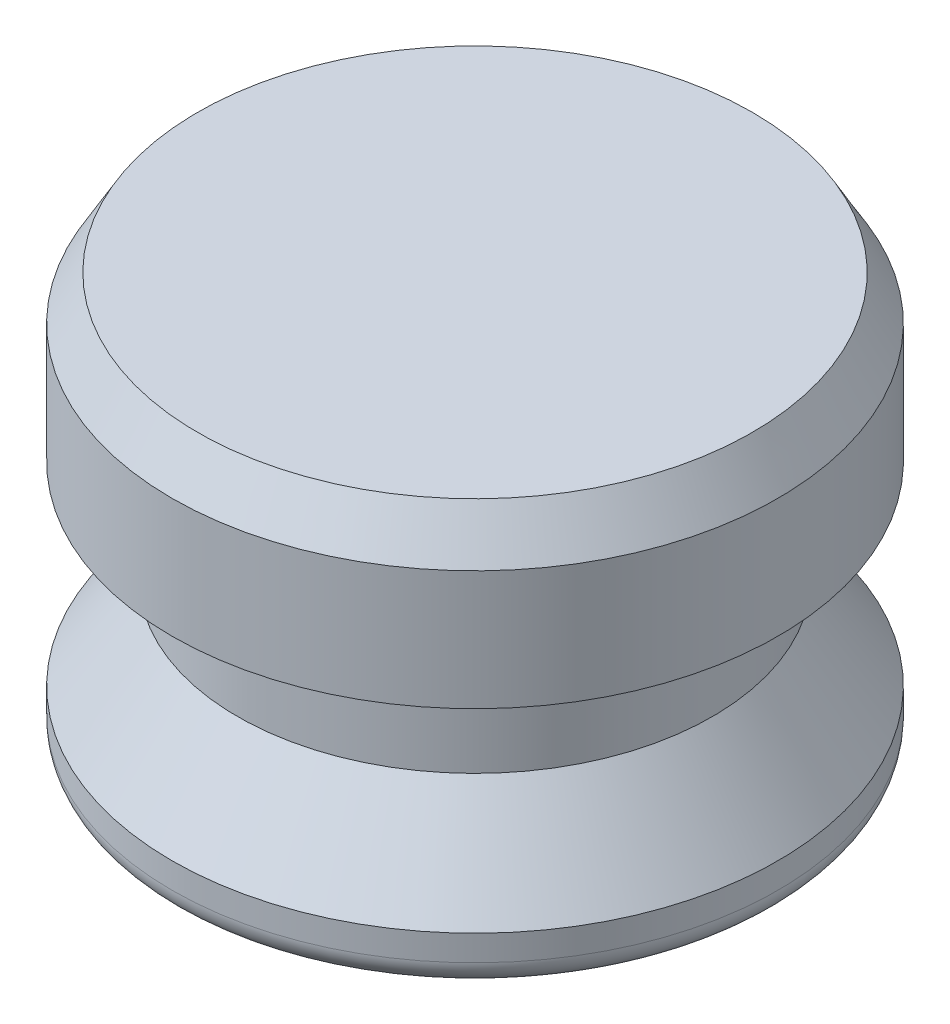
SolidWorks part; units mm, degrees
ref_plane "Front Plane" through (0, 0, 0) normal (0, 0, 1) x (1, 0, 0)
ref_plane "Top Plane" through (0, 0, 0) normal (0, 1, 0) x (1, 0, 0)
ref_plane "Right Plane" through (0, 0, 0) normal (1, 0, 0) x (0, 0, -1)
sketch "Sketch1" plane through (0, 0, 0) normal (0, 0, 1) x (1, 0, 0)
  line L0 (0, 0) -> (0, 12.7) construction
  line L1 (0, 0) -> (-9.398, 0)
  line L2 (-9.398, 0) -> (-9.398, 1.5875)
  line L4 (-7.366, 4.445) -> (-7.366, 7.62)
  line L5 (-7.366, 7.62) -> (-9.398, 7.62)
  line L6 (-9.398, 7.62) -> (-9.398, 12.7)
  line L7 (-9.398, 12.7) -> (0, 12.7)
  line L8 (-9.525, 16.6801) -> (-9.525, -9.6051) construction
  line L9 (0, 0) -> (0, 12.7)
  line L10 (-7.366, 4.445) -> (-9.398, 1.5875)
  dimension "D1" = 12.7
  dimension "D2" = 9.398
  dimension "D3" = 3.175
  dimension "D4" = 1.5875
  dimension "D5" = 9.525
  dimension "D6" = 7.366
  dimension "D7" = 7.62
revolve "Revolve1" add sketch "Sketch1" angle 360 about L9
fillet "Fillet1" radius 0.7937 1 edges at (0, 0, -9.398)
chamfer "Chamfer1" distance 0.7937 angle 60 1 edges at (0, 12.7, -9.398)
